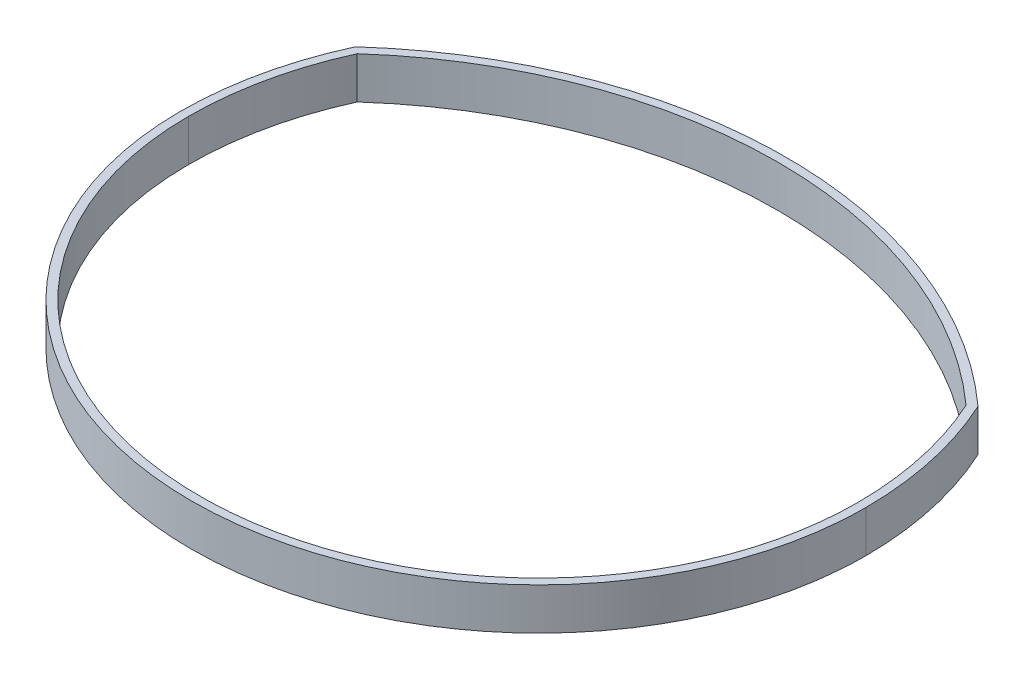
SolidWorks part; units mm, degrees
ref_plane "Front Plane" through (0, 0, 0) normal (0, 0, 1) x (1, 0, 0)
ref_plane "Top Plane" through (0, 0, 0) normal (0, 1, 0) x (1, 0, 0)
ref_plane "Right Plane" through (0, 0, 0) normal (1, 0, 0) x (0, 0, -1)
sketch "Sketch1" plane through (0, 0, 0) normal (0, 1, 0) x (1, 0, 0)
  line L0 (0, 118.5937) -> (0, 77.4941)
  arc A0 (-92.4508, 42.1356) -> (-101.6, 0) centre (0, 0) ccw
  arc A1 (92.4508, 42.1356) -> (-92.4508, 42.1356) centre (0, -61.0492) ccw
  arc A3 (101.6, 0) -> (92.4508, 42.1356) centre (0, 0) ccw
  arc A4 (94.5401, 43.6726) -> (-94.5401, 43.6726) centre (0, -61.0492) ccw
  arc A5 (-94.5401, 43.6726) -> (-104.14, 0) centre (0, 0) ccw
  arc A6 (104.14, 0) -> (94.5401, 43.6726) centre (0, 0) ccw
  ellipse E0 centre (0, 0) end of major axis (-101.6, 0) minor radius 98.1308 (-101.6, 0) -> (101.6, 0) ccw
  spline S0 degree 1 poles (-104.14, 0) (104.14, 0) knots 0 0 1 1 construction
  spline S1 degree 3 poles (-104.14, 0) (-104.14, -6.5862) (-102.7939, -19.7874) (-94.8353, -45.1445) (-75.5215, -73.0746) (-40.8558, -95.4386) (0, -103.2869) (40.8558, -95.4386) (75.5215, -73.0746) (94.8353, -45.1445) (102.7939, -19.7874) (104.14, -6.5862) (104.14, 0) knots 0 0 0 0 0.19635 0.392699 0.785398 1.178097 1.570796 1.963495 2.356194 2.748894 2.945243 3.141593 3.141593 3.141593 3.141593
  point P10 (0, -193.8272)
  point P21 (0, -98.1308)
  dimension "D2" = 2.54
  dimension "D1" = 203.2
extrude "Boss-Extrude1" add sketch "Sketch1" along normal blind 12.7
